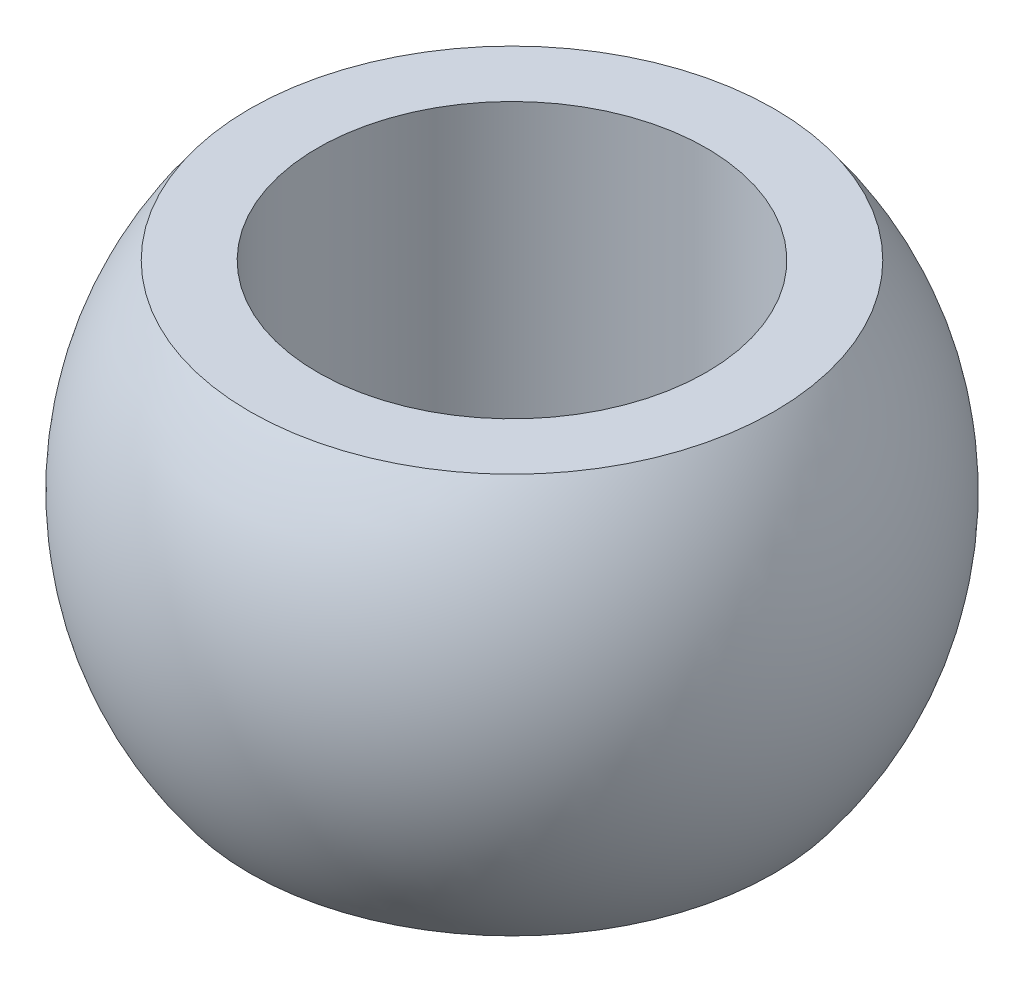
SolidWorks part; units mm, degrees
material "Brass"
ref_plane "Front Plane" through (0, 0, 0) normal (0, 0, 1) x (1, 0, 0)
ref_plane "Top Plane" through (0, 0, 0) normal (0, 1, 0) x (1, 0, 0)
ref_plane "Right Plane" through (0, 0, 0) normal (1, 0, 0) x (0, 0, -1)
sketch "Sketch1" plane through (0, 0, 0) normal (0, 0, 1) x (1, 0, 0)
  line L0 (0, -449.6439) -> (0, 22032.5529) construction
  line L1 (1.8887, 1.44) -> (1.4, 1.44)
  line L2 (1.4, 1.44) -> (1.4, -1.44)
  line L3 (1.4, -1.44) -> (1.8887, -1.44)
  arc A0 (1.8887, 1.44) -> (1.8887, -1.44) centre (0, 0) cw
  point P6 (1.4, 0)
  dimension "D2" = 2.375
  dimension "D1" = 2.8
  dimension "D3" = 2.88
revolve "Revolve1" add sketch "Sketch1" angle 360 about L0
